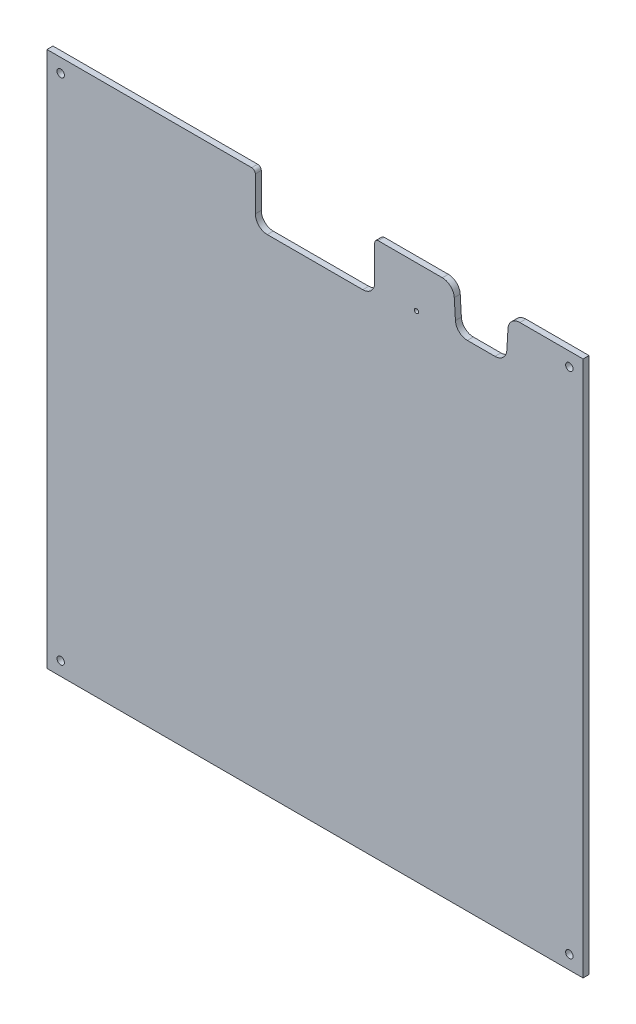
SolidWorks part; units mm, degrees
material "ABS PC"
ref_plane "Piano frontale" through (0, 0, 0) normal (0, 0, 1) x (1, 0, 0)
ref_plane "Piano superiore" through (0, 0, 0) normal (0, 1, 0) x (1, 0, 0)
ref_plane "Piano destro" through (0, 0, 0) normal (1, 0, 0) x (0, 0, -1)
sketch "Schizzo1" plane through (0, 0, 0) normal (0, 0, 1) x (1, 0, 0)
  line L0 (0, 0) -> (0, 449)
  line L1 (0, 449) -> (171.5, 449)
  line L2 (449, 449) -> (449, 0)
  line L3 (449, 0) -> (0, 0)
  line L4 (174.5, 446) -> (174.5, 417)
  line L5 (184.5, 407) -> (264.5, 407)
  line L6 (274.5, 417) -> (274.5, 446)
  line L7 (277.5, 449) -> (331.146, 449)
  line L8 (154.5, 414) -> (294.5, 414) construction
  line L9 (224.5, 379) -> (224.5, 419) construction
  line L10 (341.1283, 439.5945) -> (342.0925, 423.4055)
  line L11 (352.0748, 414) -> (375.1818, 414)
  line L12 (363.6283, 414) -> (363.6283, 449) construction
  line L13 (0, 224.5) -> (449, 224.5) construction
  line L14 (386.1283, 439.5945) -> (385.1641, 423.4055)
  line L15 (396.1106, 449) -> (449, 449)
  line L23 (73.9219, 399) -> (73.9219, 449) construction
  line L24 (174.5, 431.5) -> (314.5, 431.5) construction
  arc A0 (174.5, 417) -> (184.5, 407) centre (184.5, 417) ccw
  arc A1 (274.5, 417) -> (264.5, 407) centre (264.5, 417) cw
  circle A2 centre (11.5, 11.5) radius 3.1
  circle A3 centre (437.5, 11.5) radius 3.1
  circle A4 centre (437.5, 437.5) radius 3.1
  circle A5 centre (11.5, 437.5) radius 3.1
  circle A6 centre (309.5, 414) radius 1.75
  arc A7 (277.5, 449) -> (274.5, 446) centre (277.5, 446) ccw
  arc A8 (342.0925, 423.4055) -> (352.0748, 414) centre (352.0748, 424) ccw
  arc A9 (375.1818, 414) -> (385.1641, 423.4055) centre (375.1818, 424) ccw
  arc A10 (174.5, 446) -> (171.5, 449) centre (171.5, 446) ccw
  arc A11 (386.1283, 439.5945) -> (396.1106, 449) centre (396.1106, 439) cw
  arc A12 (341.1283, 439.5945) -> (331.146, 449) centre (331.146, 439) ccw
  point P11 (174.5, 407)
  point P14 (274.5, 407)
  point P44 (174.5, 449)
  point P46 (342.6527, 414)
  point P49 (384.6039, 414)
  point P52 (386.6885, 449)
  point P55 (340.5681, 449)
  dimension "D5" = 10
  dimension "D6" = 11.5
  dimension "D7" = 11.5
  dimension "D8" = 6.2
  dimension "D9" = 3.5
  dimension "D10" = 35
  dimension "D12" = 3
  dimension "D11" = 10
  dimension "D1" = 449
  dimension "D2" = 449
  dimension "D3" = 100
  dimension "D4" = 42
  dimension "D13" = 45
  dimension "D21" = 35
extrude "Estrusione-Estrusione1" add sketch "Schizzo1" along normal blind 5
